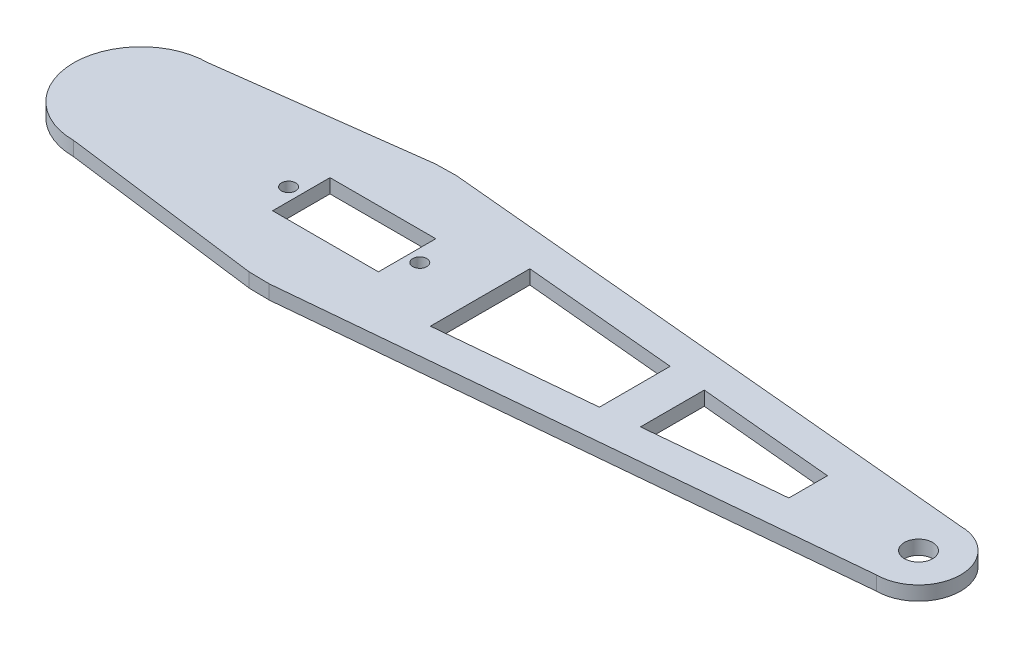
SolidWorks part; units mm, degrees
ref_plane "Front Plane" through (0, 0, 0) normal (0, 0, 1) x (1, 0, 0)
ref_plane "Top Plane" through (0, 0, 0) normal (0, 1, 0) x (1, 0, 0)
ref_plane "Right Plane" through (0, 0, 0) normal (1, 0, 0) x (0, 0, -1)
other "Center of Mass"
sketch "Sketch1" plane through (0, 0, 0) normal (0, 1, 0) x (1, 0, 0)
  line L1 (1.8468, 19.9146) -> (120, 8.9578)
  line L7 (-2.5659, -19.8347) -> (1.8468, -19.9146)
  line L8 (-11.25, 6.1) -> (11.25, 6.1)
  line L9 (-11.25, 6.1) -> (-11.25, -6.1)
  line L10 (-11.25, -6.1) -> (11.25, -6.1)
  line L11 (11.25, 6.1) -> (11.25, -6.1)
  line L12 (-11.25, 6.1) -> (11.25, -6.1) construction
  line L13 (-11.25, -6.1) -> (11.25, 6.1) construction
  line L14 (120, -8.9578) -> (1.8468, -19.9146)
  line L15 (-45.3435, 14.3009) -> (-2.5659, 19.8347)
  line L16 (-45.3435, -14.3009) -> (-2.5659, -19.8347)
  line L17 (-2.5659, 19.8347) -> (1.8468, 19.9146)
  line L18 (96.5292, 4.1043) -> (67.6603, 6.7814)
  line L19 (96.5292, -4.1043) -> (67.6603, -6.7814)
  line L20 (96.5292, 4.1043) -> (96.5292, -4.1043)
  line L21 (67.6603, 6.7814) -> (67.6603, -6.7814)
  line L22 (59.6591, 7.5234) -> (26.7796, 10.5724)
  line L23 (26.7796, 10.5724) -> (26.7796, -10.5724)
  line L24 (26.7796, -10.5724) -> (59.6591, -7.5234)
  line L25 (59.6591, -7.5234) -> (59.6591, 7.5234)
  circle A5 centre (13.95, 0) radius 1.5
  circle A6 centre (-13.95, 0) radius 1.5
  circle A7 centre (0, 0) radius 20 construction
  circle A8 centre (120, 0) radius 8.9578 construction
  arc A9 (120, 8.9578) -> (120, -8.9578) centre (120, 0) cw
  circle A10 centre (-45.3435, 0) radius 14.3009 construction
  arc A11 (-45.3435, 14.3009) -> (-45.3435, -14.3009) centre (-45.3435, 0) ccw
  circle A12 centre (120, 0) radius 3
  dimension "D5" = 3
  dimension "D6" = 3
  dimension "D7" = 40
  dimension "D13" = 6
  dimension "D1" = 22.5
  dimension "D2" = 12.2
  dimension "D3" = 2.7
  dimension "D4" = 2.7
  dimension "D8" = 120
  dimension "D9" = 7
  dimension "D10" = 7
  dimension "D11" = 7
  dimension "D12" = 7
extrude "Boss-Extrude1" add sketch "Sketch1" along normal blind 3
